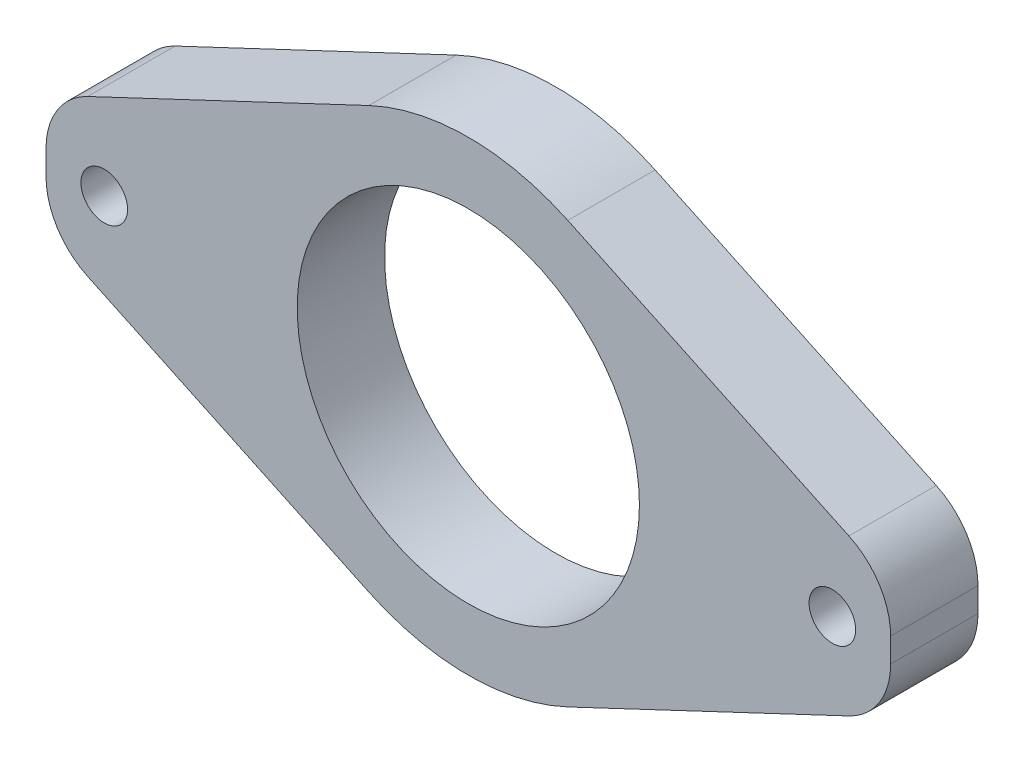
SolidWorks part; units mm, degrees
material "MDF"
ref_plane "Plano frontal" through (0, 0, 0) normal (0, 0, 1) x (1, 0, 0)
ref_plane "Plano superior" through (0, 0, 0) normal (0, 1, 0) x (1, 0, 0)
ref_plane "Plano direito" through (0, 0, 0) normal (1, 0, 0) x (0, 0, -1)
sketch "Esboço1" plane through (0, 0, 0) normal (0, 0, 1) x (1, 0, 0)
  line L0 (-19.5214, 0) -> (-12, 0) construction
  line L1 (-25, 0) -> (25, 0) construction
  line L2 (-29, 4) -> (-15.4919, 4)
  line L3 (0, 0) -> (0, 11.75) construction
  line L4 (29, 4) -> (15.4919, 4)
  line L5 (29, -4) -> (15.4919, -4)
  line L6 (-29, -4) -> (-15.4919, -4)
  line L7 (-29, -4) -> (-29, 4)
  line L8 (29, 4) -> (29, -4)
  line L9 (-29, -4) -> (-6.832, -14.468)
  line L10 (-29, 4) -> (-6.832, 14.468)
  line L11 (29, 4) -> (6.832, 14.468)
  line L12 (29, -4) -> (6.832, -14.468)
  circle A0 centre (0, 0) radius 11.75
  circle A1 centre (0, 0) radius 12 construction
  circle A3 centre (-25, 0) radius 1.6
  circle A4 centre (25, 0) radius 1.6
  arc A5 (-15.4919, 4) -> (15.4919, 4) centre (0, 0) cw
  arc A6 (-15.4919, -4) -> (15.4919, -4) centre (0, 0) ccw
  circle A7 centre (-13.5, 0) radius 3 construction
  point P5 (-12, 0)
  point P6 (-19.5214, 0)
  point P18 (0, 16)
  point P22 (0, 12)
  point P23 (0, 11.75)
  dimension "D1" = 23.5
  dimension "D2" = 24
  dimension "D3" = 3.2
  dimension "D7" = 16
  dimension "D4" = 6
  dimension "D8" = 27
  dimension "D5" = 4
  dimension "D6" = 4
  dimension "D9" = 50
extrude "Ressalto-extrusão1" add sketch "Esboço1" along normal blind 6 contours A6 L6 L9 | L6 A6 L5 L8 L4 A5 L2 L7 A0 A3 A4 | L2 A5 L10 | L11 A5 L4 | A6 L12 L5
fillet "Filete3" radius 5 4 edges at (29, 4, 3) (29, -4, 3) (-29, 4, 3) (-29, -4, 3)
